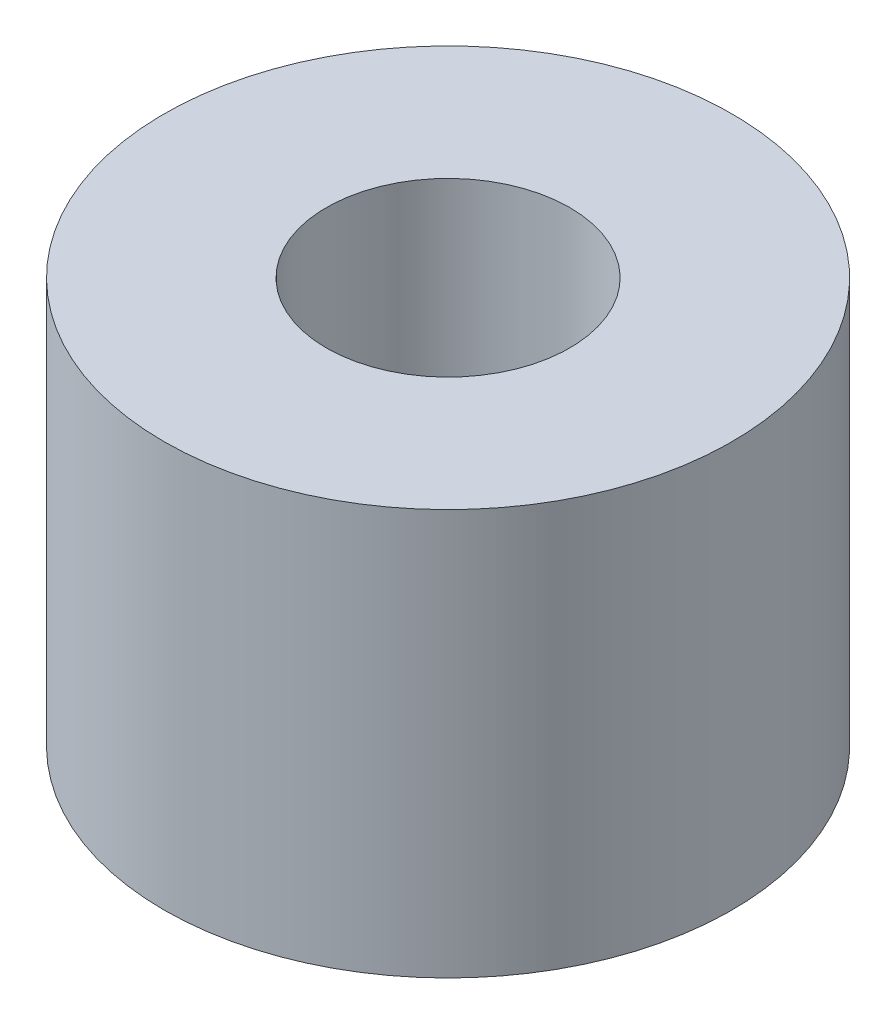
SolidWorks part; units mm, degrees
ref_plane "Front Plane" through (0, 0, 0) normal (0, 0, 1) x (1, 0, 0)
ref_plane "Top Plane" through (0, 0, 0) normal (0, 1, 0) x (1, 0, 0)
ref_plane "Right Plane" through (0, 0, 0) normal (1, 0, 0) x (0, 0, -1)
sketch "Sketch2" plane through (0, 0, 0) normal (0, 1, 0) x (1, 0, 0)
  circle A0 centre (0, 0) radius 1.5
  circle A1 centre (0, 0) radius 3.5
  dimension "D1" = 3
  dimension "D2" = 7
extrude "Boss-Extrude1" add sketch "Sketch2" along normal blind 5
